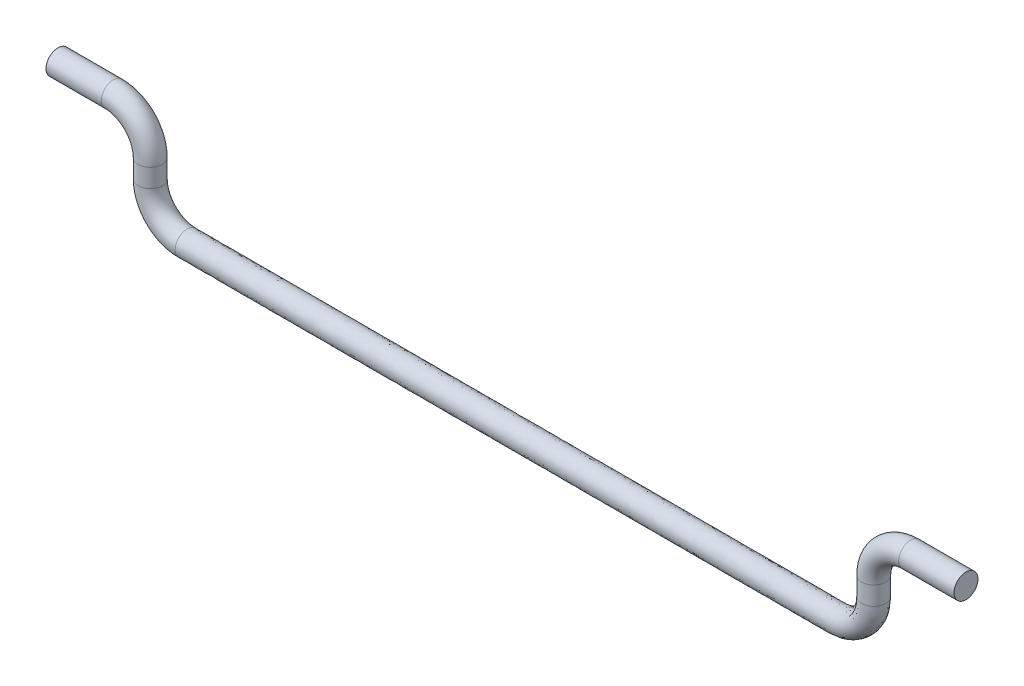
SolidWorks part; units mm, degrees
ref_plane "Front Plane" through (0, 0, 0) normal (0, 0, 1) x (1, 0, 0)
ref_plane "Top Plane" through (0, 0, 0) normal (0, 1, 0) x (1, 0, 0)
ref_plane "Right Plane" through (0, 0, 0) normal (1, 0, 0) x (0, 0, -1)
sketch "Sketch1" plane through (0, 0, 0) normal (0, 0, 1) x (1, 0, 0)
  line L0 (0, 0) -> (35.2, 0)
  line L1 (-2, 2) -> (-2, 3)
  line L2 (-4, 5) -> (-7, 5)
  line L3 (37.2, 2) -> (37.2, 3)
  line L4 (39.2, 5) -> (42.2, 5)
  arc A0 (0, 0) -> (-2, 2) centre (0, 2) cw
  arc A1 (-2, 3) -> (-4, 5) centre (-4, 3) ccw
  arc A2 (35.2, 0) -> (37.2, 2) centre (35.2, 2) ccw
  arc A3 (37.2, 3) -> (39.2, 5) centre (39.2, 3) cw
  point P14 (37.6683, 2)
  dimension "D2" = 1
  dimension "D3" = 2
  dimension "D1" = 39.2
  dimension "D5" = 3
ref_plane "Plane1" through (35.2, 0, 0) normal (1, 0, 0) x (0, 0, -1)
sketch "Sketch2" plane through (35.2, 0, 0) normal (1, 0, 0) x (0, 0, -1)
  circle A0 centre (0, 0) radius 0.65
  dimension "D1" = 1.3
sweep "Sweep1" add profiles "Sketch2" path "Sketch1"
